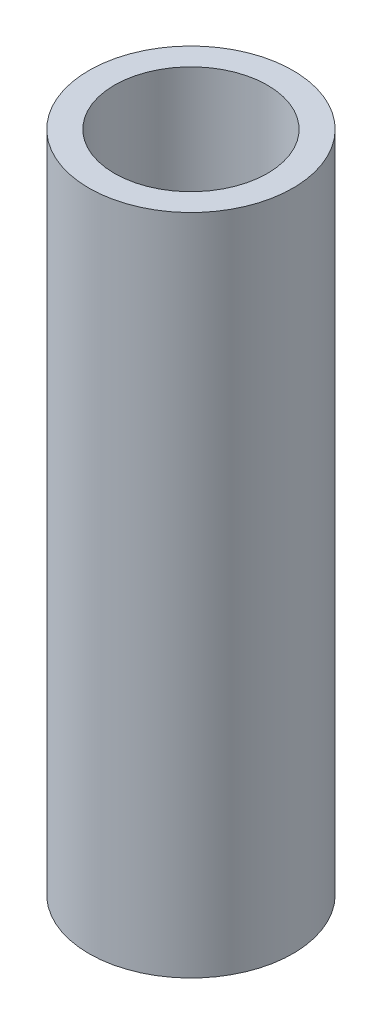
SolidWorks part; units mm, degrees
ref_plane "Front Plane" through (0, 0, 0) normal (0, 0, 1) x (1, 0, 0)
ref_plane "Top Plane" through (0, 0, 0) normal (0, 1, 0) x (1, 0, 0)
ref_plane "Right Plane" through (0, 0, 0) normal (1, 0, 0) x (0, 0, -1)
sketch "Sketch1" plane through (0, 0, 0) normal (0, 1, 0) x (1, 0, 0)
  circle A0 centre (0, 0) radius 4
  circle A1 centre (0, 0) radius 3
  dimension "D1" = 8
  dimension "D2" = 6
extrude "Boss-Extrude1" add sketch "Sketch1" along normal blind 26
